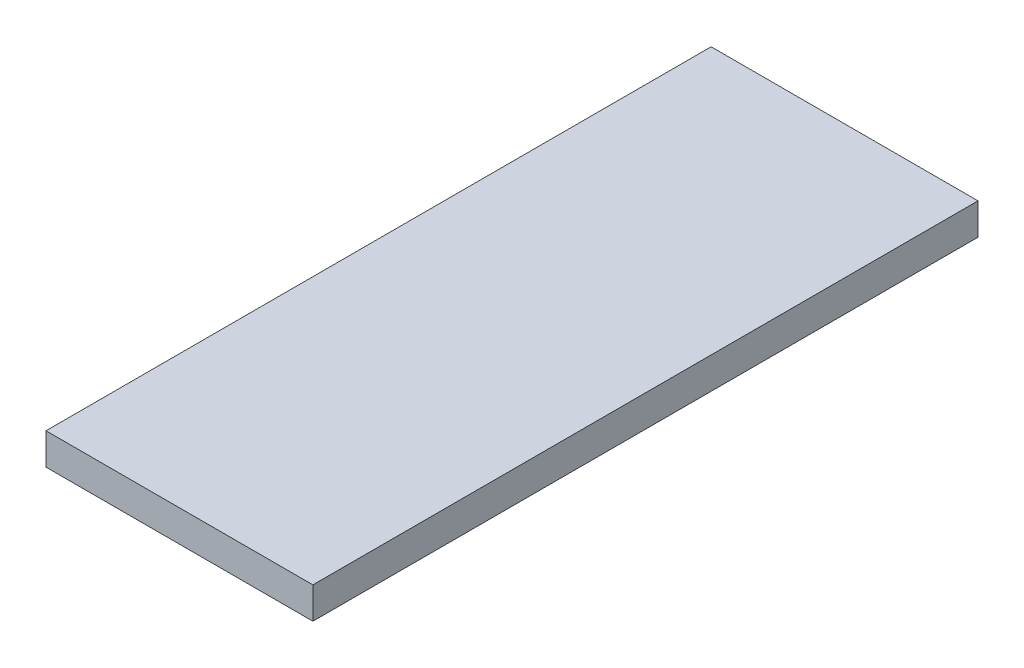
SolidWorks part; units mm, degrees
ref_plane "Front Plane" through (0, 0, 0) normal (0, 0, 1) x (1, 0, 0)
ref_plane "Top Plane" through (0, 0, 0) normal (0, 1, 0) x (1, 0, 0)
ref_plane "Right Plane" through (0, 0, 0) normal (1, 0, 0) x (0, 0, -1)
sketch "Sketch1" plane through (0, 0, 0) normal (0, 1, 0) x (1, 0, 0)
  line L1 (-12.7, 31.65) -> (12.7, 31.65)
  line L2 (-12.7, 31.65) -> (-12.7, -31.65)
  line L3 (-12.7, -31.65) -> (12.7, -31.65)
  line L4 (12.7, 31.65) -> (12.7, -31.65)
  line L5 (-12.7, 31.65) -> (12.7, -31.65) construction
  line L6 (-12.7, -31.65) -> (12.7, 31.65) construction
  point P0 (0, 0)
  dimension "D1" = 63.3
  dimension "D2" = 25.4
extrude "Boss-Extrude1" add sketch "Sketch1" along normal blind 3
